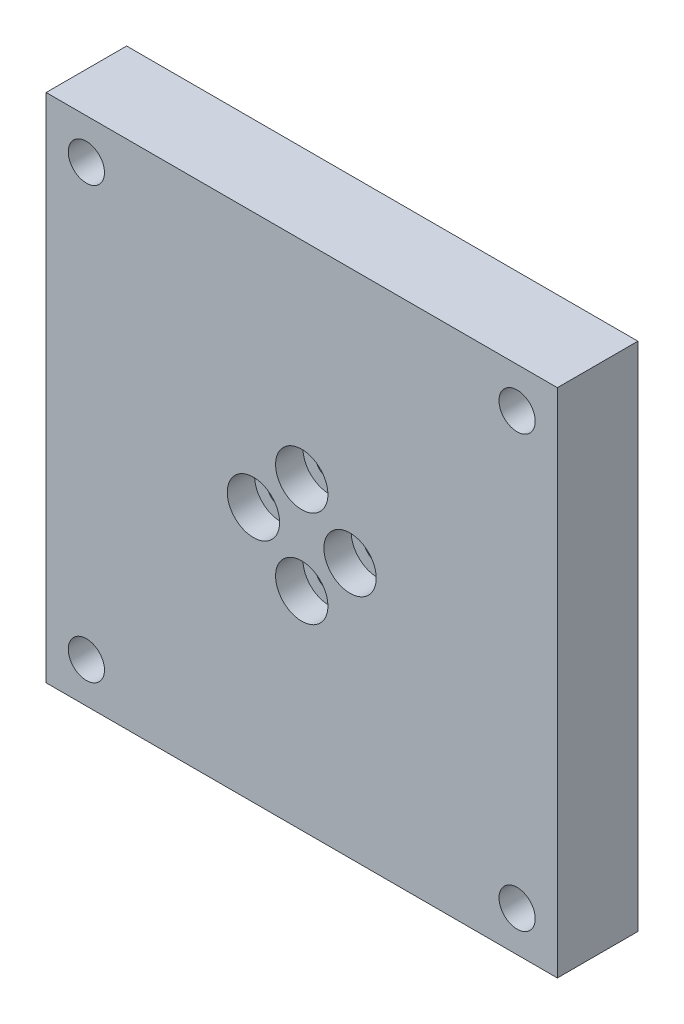
SolidWorks part; units mm, degrees
material "Сплав 2024"
ref_plane "Спереди" through (0, 0, 0) normal (0, 0, 1) x (1, 0, 0)
ref_plane "Сверху" through (0, 0, 0) normal (0, 1, 0) x (1, 0, 0)
ref_plane "Справа" through (0, 0, 0) normal (1, 0, 0) x (0, 0, -1)
sketch "Эскиз1" plane through (0, 0, 0) normal (0, 0, 1) x (1, 0, 0)
  line L1 (-31.75, 31.75) -> (31.75, 31.75)
  line L2 (-31.75, 31.75) -> (-31.75, -31.75)
  line L3 (-31.75, -31.75) -> (31.75, -31.75)
  line L4 (31.75, 31.75) -> (31.75, -31.75)
  line L5 (-31.75, 31.75) -> (31.75, -31.75) construction
  line L6 (-31.75, -31.75) -> (31.75, 31.75) construction
  point P0 (0, 0)
  dimension "D1" = 63.5
  dimension "D2" = 63.5
extrude "Бобышка-Вытянуть1" add sketch "Эскиз1" along normal blind 10
sketch "Эскиз2" plane through (0, 0, 10) normal (0, 0, 1) x (1, 0, 0)
  line L0 (-26.75, 31.75) -> (-26.75, -31.75) construction
  line L1 (31.75, 31.75) -> (-31.75, 31.75) construction
  line L2 (-31.75, -31.75) -> (31.75, -31.75) construction
  line L3 (26.75, 31.75) -> (26.75, -31.75) construction
  line L4 (-31.75, 26.75) -> (31.75, 26.75) construction
  line L5 (-31.75, 31.75) -> (-31.75, -31.75) construction
  line L6 (31.75, -31.75) -> (31.75, 31.75) construction
  line L7 (31.75, -26.75) -> (-31.75, -26.75) construction
  line L8 (0, 31.75) -> (0, -31.75) construction
  line L9 (-31.75, 0) -> (31.75, 0) construction
  circle A0 centre (0, 0) radius 6 construction
  dimension "D5" = 12
  dimension "D1" = 5
  dimension "D2" = 5
  dimension "D3" = 5
  dimension "D4" = 5
hole_wizard "Цековка для винта с внутренним шестигранником M31" positions "Эскиз4" profile "Эскиз3" counterbore size "M3" standard "Din" end condition through all
sketch "Эскиз4" plane through (0, 0, 10) normal (0, 0, 1) x (1, 0, 0)
  line L0 (0, 31.75) -> (0, -31.75) construction
  line L1 (-31.75, 0) -> (31.75, 0) construction
  circle A0 centre (0, 0) radius 6 construction
  point P0 (0, 6)
  point P6 (-6, 0)
  point P10 (0, -6)
  point P12 (6, 0)
sketch "Эскиз3" plane through (0, 6, 10) normal (1, 0, 0) x (0, -1, 0)
  line L0 (0, 0) -> (0, 10)
  line L1 (0, 10) -> (1.7, 10)
  line L3 (1.7, 10) -> (1.7, 3.4)
  line L4 (1.7, 3.4) -> (3.25, 3.4)
  line L5 (3.25, 3.4) -> (3.25, 0)
  line L7 (3.25, 0) -> (0, 0)
  line L11 (0, -6.35) -> (0, 107.95) construction
  dimension "Диаметр сквозного отверстия" = 3.4
  dimension "Глубина сквозного отверстия" = 10
  dimension "Диаметр цековки" = 6.5
  dimension "Глубина цековки" = 3.4
hole_wizard "Цековка для винта с внутренним шестигранником M41" positions "Эскиз6" profile "Эскиз5" counterbore size "M4" standard "Din" end condition through all
sketch "Эскиз6" plane through (0, 0, 0) normal (0, 0, -1) x (-1, 0, 0)
  line L0 (-26.75, 31.75) -> (-26.75, -31.75) construction
  line L1 (31.75, 26.75) -> (-31.75, 26.75) construction
  line L2 (-31.75, -26.75) -> (31.75, -26.75) construction
  line L3 (26.75, 31.75) -> (26.75, -31.75) construction
  point P0 (-26.75, 26.75)
  point P6 (-26.75, -26.75)
  point P10 (26.75, -26.75)
  point P14 (26.75, 26.75)
sketch "Эскиз5" plane through (26.75, 26.75, 0) normal (1, 0, 0) x (0, 1, 0)
  line L0 (0, 0) -> (0, 10)
  line L1 (0, 10) -> (2.25, 10)
  line L3 (2.25, 10) -> (2.25, 4.4)
  line L4 (2.25, 4.4) -> (4, 4.4)
  line L5 (4, 4.4) -> (4, 0)
  line L7 (4, 0) -> (0, 0)
  line L11 (0, -6.35) -> (0, 107.95) construction
  dimension "Диаметр сквозного отверстия" = 4.5
  dimension "Глубина сквозного отверстия" = 10
  dimension "Диаметр цековки" = 8
  dimension "Глубина цековки" = 4.4
sketch "Эскиз8" plane through (0, 0, 0) normal (0, 0, -1) x (-1, 0, 0)
  line L8 (-28.75, 28.75) -> (-28.75, -28.75)
  line L9 (28.75, 28.75) -> (-28.75, 28.75)
  line L10 (28.75, -28.75) -> (28.75, 28.75)
  line L11 (-28.75, -28.75) -> (28.75, -28.75)
  line L12 (-28.75, 16.8001) -> (-28.75, -16.8001)
  line L13 (16.8001, 28.75) -> (-16.8001, 28.75)
  line L14 (28.75, -16.8001) -> (28.75, 16.8001)
  line L15 (-16.8001, -28.75) -> (16.8001, -28.75)
  circle A31 centre (-26.75, 26.75) radius 7
  arc A32 (-26.05, 19.7851) -> (-19.7851, 26.05) centre (-26.75, 26.75) ccw
  circle A34 centre (26.75, 26.75) radius 7
  arc A35 (19.7851, 26.05) -> (26.05, 19.7851) centre (26.75, 26.75) ccw
  circle A37 centre (26.75, -26.75) radius 7
  arc A38 (26.05, -19.7851) -> (19.7851, -26.05) centre (26.75, -26.75) ccw
  arc A39 (-28.75, 16.8001) -> (-26.05, 19.7851) centre (-25.75, 16.8001) cw
  circle A40 centre (-26.75, -26.75) radius 7
  arc A41 (-19.7851, -26.05) -> (-26.05, -19.7851) centre (-26.75, -26.75) ccw
  arc A42 (-26.05, -19.7851) -> (-28.75, -16.8001) centre (-25.75, -16.8001) cw
  arc A43 (-16.8001, -28.75) -> (-19.7851, -26.05) centre (-16.8001, -25.75) cw
  arc A44 (19.7851, -26.05) -> (16.8001, -28.75) centre (16.8001, -25.75) cw
  arc A45 (28.75, -16.8001) -> (26.05, -19.7851) centre (25.75, -16.8001) cw
  arc A46 (26.05, 19.7851) -> (28.75, 16.8001) centre (25.75, 16.8001) cw
  arc A47 (16.8001, 28.75) -> (19.7851, 26.05) centre (16.8001, 25.75) cw
  arc A48 (-19.7851, 26.05) -> (-16.8001, 28.75) centre (-16.8001, 25.75) cw
  circle A49 centre (0, 0) radius 12.5
  dimension "D6" = 3
  dimension "D7" = 3
  dimension "D8" = 25
  dimension "D1" = 3
  dimension "D2" = 3
  dimension "D3" = 3
  dimension "D4" = 3
  dimension "D5" = 3
extrude "Вырез-Вытянуть1" cut sketch "Эскиз8" against normal offset from surface (7 mm away) 3 up to face at (24.5, 26.75, 10)
sketch "Эскиз9" plane through (0, 0, 7) normal (0, 0, -1) x (-1, 0, 0)
  line L0 (-26.75, 26.75) -> (26.75, -26.75) construction
  line L1 (26.75, 26.75) -> (-26.75, -26.75) construction
  line L2 (20.8546, 22.9759) -> (7.7143, 9.8356)
  line L3 (-22.9759, 20.8546) -> (-9.8356, 7.7143)
  line L4 (22.9759, 20.8546) -> (9.8356, 7.7143)
  line L5 (-20.8546, 22.9759) -> (-7.7143, 9.8356)
  line L8 (-25.6893, 27.8107) -> (27.8107, -25.6893) construction
  line L10 (-27.8107, 25.6893) -> (25.6893, -27.8107) construction
  line L12 (27.8107, 25.6893) -> (-25.6893, -27.8107) construction
  line L13 (7.7143, -9.8356) -> (20.8546, -22.9759)
  line L14 (25.6893, 27.8107) -> (-27.8107, -25.6893) construction
  line L15 (9.8356, -7.7143) -> (22.9759, -20.8546)
  line L16 (-7.7143, -9.8356) -> (-20.8546, -22.9759)
  line L17 (-9.8356, -7.7143) -> (-22.9759, -20.8546)
  circle A0 centre (0, 0) radius 12.5 construction
  arc A1 (-7.7143, 9.8356) -> (-9.8356, 7.7143) centre (0, 0) ccw
  arc A2 (-26.05, 19.7851) -> (-19.7851, 26.05) centre (-26.75, 26.75) ccw construction
  arc A3 (19.7851, 26.05) -> (26.05, 19.7851) centre (26.75, 26.75) ccw construction
  arc A4 (26.05, -19.7851) -> (19.7851, -26.05) centre (26.75, -26.75) ccw construction
  arc A5 (-19.7851, -26.05) -> (-26.05, -19.7851) centre (-26.75, -26.75) ccw construction
  arc A6 (-22.9759, 20.8546) -> (-20.8546, 22.9759) centre (-26.75, 26.75) ccw
  arc A7 (20.8546, 22.9759) -> (22.9759, 20.8546) centre (26.75, 26.75) ccw
  arc A8 (22.9759, -20.8546) -> (20.8546, -22.9759) centre (26.75, -26.75) ccw
  arc A9 (-20.8546, -22.9759) -> (-22.9759, -20.8546) centre (-26.75, -26.75) ccw
  arc A10 (-9.8356, -7.7143) -> (-7.7143, -9.8356) centre (0, 0) ccw
  arc A11 (9.8356, 7.7143) -> (7.7143, 9.8356) centre (0, 0) ccw
  arc A12 (7.7143, -9.8356) -> (9.8356, -7.7143) centre (0, 0) ccw
  dimension "D1" = 1.5
  dimension "D2" = 1.5
extrude "Бобышка-Вытянуть2" add sketch "Эскиз9" along normal up to surface (7 mm away) up to face at (7.7, 0, 0)
fillet "Скругление1" radius 3 16 edges at (22.9759, 20.8546, 3.5) (9.8356, 7.7143, 3.5) (9.8356, -7.7143, 3.5) (22.9759, -20.8546, 3.5) (20.8546, -22.9759, 3.5) (7.7143, -9.8356, 3.5) (-7.7143, -9.8356, 3.5) (-20.8546, -22.9759, 3.5) (-22.9759, -20.8546, 3.5) (-9.8356, -7.7143, 3.5) (-9.8356, 7.7143, 3.5) (20.8546, 22.9759, 3.5) (7.7143, 9.8356, 3.5) (-7.7143, 9.8356, 3.5) (-22.9759, 20.8546, 3.5) (-20.8546, 22.9759, 3.5)
fillet "Скругление2" [suppressed] radius 0.1
